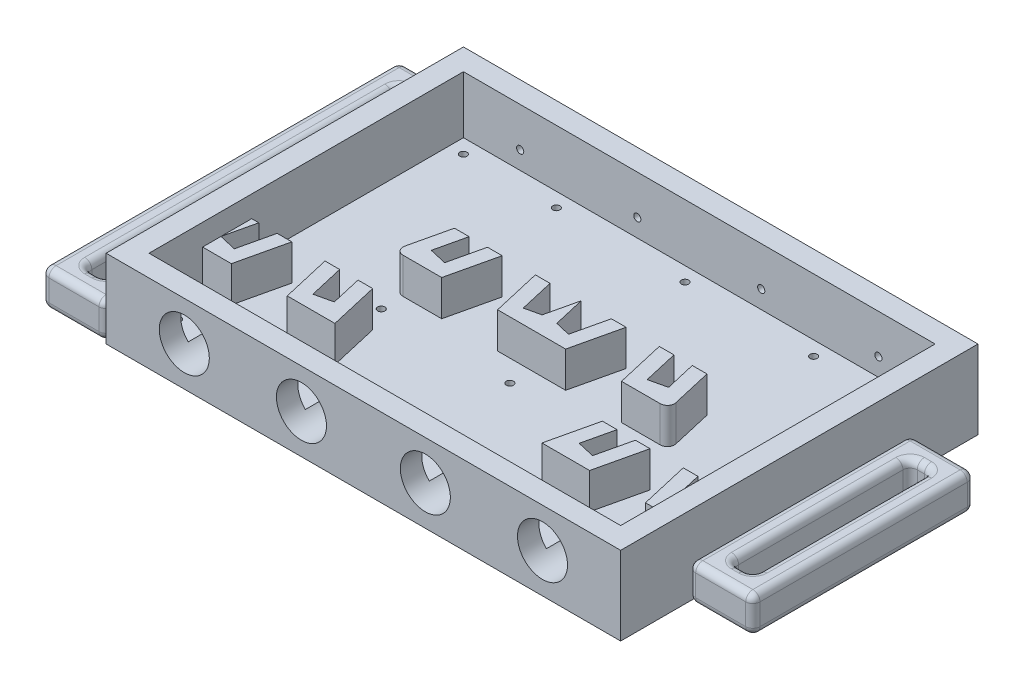
SolidWorks part; units mm, degrees
ref_plane "Front Plane" through (0, 0, 0) normal (0, 0, 1) x (1, 0, 0)
ref_plane "Top Plane" through (0, 0, 0) normal (0, 1, 0) x (1, 0, 0)
ref_plane "Right Plane" through (0, 0, 0) normal (1, 0, 0) x (0, 0, -1)
sketch "Sketch1" plane through (0, 0, 0) normal (0, 1, 0) x (1, 0, 0)
  line L1 (0, 0) -> (72, 0)
  line L2 (0, 0) -> (0, 50)
  line L3 (0, 50) -> (72, 50)
  line L4 (72, 0) -> (72, 50)
extrude "Boss-Extrude2" add sketch "Sketch1" along normal blind 11 contours L3 L4 L1 L2
sketch "Sketch2" plane through (0, 11, 0) normal (0, 1, 0) x (1, 0, 0)
  line L0 (0, 50) -> (72, 50) construction
  line L1 (3, 3) -> (69, 3)
  line L2 (3, 3) -> (3, 47)
  line L3 (3, 47) -> (69, 47)
  line L4 (69, 3) -> (69, 47)
  line L6 (0, 0) -> (72, 0) construction
  line L7 (0, 0) -> (0, 50) construction
  line L8 (72, 0) -> (72, 50) construction
  dimension "D1" = 3
  dimension "D2" = 3
  dimension "D3" = 3
  dimension "D4" = 3
extrude "Cut-Extrude1" cut sketch "Sketch2" against normal blind 8
sketch "Sketch3" plane through (0, 3, 0) normal (0, 1, 0) x (1, 0, 0)
  line L0 (0.3558, 10.5) -> (7.0268, 10.5)
  line L1 (14.8431, 10.5) -> (21.5141, 10.5)
  line L2 (1.9423, 17.3719) -> (8.6133, 17.3719)
  line L3 (13.2566, 17.3719) -> (19.9276, 17.3719)
  line L4 (1.9423, 17.3719) -> (0.3558, 10.5)
  line L5 (8.6133, 17.3719) -> (7.0268, 10.5)
  line L6 (3.9949, 17.3719) -> (3, 13.0624)
  line L7 (3, 13.0624) -> (5.4359, 12.5)
  line L8 (5.4359, 12.5) -> (6.5607, 17.3719)
  line L9 (13.2566, 17.3719) -> (14.8431, 10.5)
  line L10 (19.9276, 17.3719) -> (21.5141, 10.5)
  line L11 (18.8699, 13.0624) -> (14.3709, 32.5498)
  line L12 (17.875, 17.3719) -> (18.8699, 13.0624)
  line L13 (18.8699, 13.0624) -> (16.434, 12.5)
  line L14 (16.434, 12.5) -> (15.3092, 17.3719)
  line L15 (16.7514, 23.5375) -> (23.4224, 23.5375)
  line L16 (31.2406, 23.5375) -> (37.6037, 23.5375)
  line L17 (18.3379, 30.4094) -> (25.0089, 30.4094)
  line L18 (29.6541, 30.4094) -> (36.0172, 30.4094)
  line L19 (18.3379, 30.4094) -> (16.7514, 23.5375)
  line L20 (25.0089, 30.4094) -> (23.4224, 23.5375)
  line L21 (20.3905, 30.4094) -> (19.3956, 26.0999)
  line L22 (19.3956, 26.0999) -> (21.8315, 25.5375)
  line L23 (21.8315, 25.5375) -> (22.9563, 30.4094)
  line L24 (29.6541, 30.4094) -> (31.2406, 23.5375)
  line L25 (36.0172, 30.4094) -> (37.6037, 23.5375)
  line L26 (33.9646, 30.4094) -> (34.9751, 26.0324)
  line L27 (34.9751, 26.0324) -> (32.8315, 25.5375)
  line L28 (32.8315, 25.5375) -> (31.7067, 30.4094)
  line L29 (50.484, 10.5) -> (57.1549, 10.5)
  line L30 (64.9732, 10.5) -> (71.6442, 10.5)
  line L31 (52.0705, 17.3719) -> (58.7414, 17.3719)
  line L32 (63.3867, 17.3719) -> (70.0577, 17.3719)
  line L33 (52.0705, 17.3719) -> (50.484, 10.5)
  line L34 (58.7414, 17.3719) -> (57.1549, 10.5)
  line L35 (54.1231, 17.3719) -> (53.1281, 13.0624)
  line L36 (53.1281, 13.0624) -> (55.5641, 12.5)
  line L37 (55.5641, 12.5) -> (56.6888, 17.3719)
  line L38 (63.3867, 17.3719) -> (64.9732, 10.5)
  line L39 (70.0577, 17.3719) -> (71.6442, 10.5)
  line L40 (68.0051, 17.3719) -> (69, 13.0624)
  line L41 (69, 13.0624) -> (66.5641, 12.5)
  line L42 (66.5641, 12.5) -> (65.4393, 17.3719)
  line L43 (34.3991, 23.5375) -> (40.7622, 23.5375)
  line L44 (48.5805, 23.5375) -> (55.2514, 23.5375)
  line L45 (35.9856, 30.4094) -> (42.3487, 30.4094)
  line L46 (46.994, 30.4094) -> (53.6649, 30.4094)
  line L47 (35.9856, 30.4094) -> (34.3991, 23.5375)
  line L48 (42.3487, 30.4094) -> (40.7622, 23.5375)
  line L49 (38.0382, 30.4094) -> (37.0277, 26.0324)
  line L50 (37.0277, 26.0324) -> (39.1713, 25.5375)
  line L51 (39.1713, 25.5375) -> (40.2961, 30.4094)
  line L52 (46.994, 30.4094) -> (48.5805, 23.5375)
  line L53 (53.6649, 30.4094) -> (55.2514, 23.5375)
  line L54 (51.6123, 30.4094) -> (52.6073, 26.0999)
  line L55 (52.6073, 26.0999) -> (50.1713, 25.5375)
  line L56 (50.1713, 25.5375) -> (49.0466, 30.4094)
  line L57 (3, 47) -> (3, 3) construction
  line L58 (69, 3) -> (69, 47) construction
  line L59 (53.1281, 13.0624) -> (57.6272, 32.5498)
  line L60 (21.8315, 25.5375) -> (26.3305, 45.0249)
  line L61 (50.1713, 25.5375) -> (45.6723, 45.0249)
  line L62 (3, 3) -> (69, 3) construction
  line L64 (5.4359, 12.5) -> (9.9349, 31.9874)
  line L65 (16.434, 12.5) -> (11.9349, 31.9874)
  line L66 (0, 0) -> (0, 50) construction
  line M1 (3, 47) -> (3, 3)
  line M3 (69, 3) -> (69, 47)
  dimension "D2" = 77
  dimension "D3" = 2.5
  dimension "D4" = 2
  dimension "D5" = 2
  dimension "D6" = 2.5
  dimension "D7" = 2
  dimension "D8" = 2
  dimension "D9" = 5
  dimension "D10" = 5
  dimension "D11" = 77
  dimension "D12" = 2
  dimension "D13" = 2
  dimension "D14" = 2.5
  dimension "D15" = 2
  dimension "D16" = 2
  dimension "D17" = 11
  dimension "D18" = 77
  dimension "D19" = 77
  dimension "D20" = 5
  dimension "D21" = 5
  dimension "D22" = 2
  dimension "D23" = 2.2
  dimension "D24" = 2
  dimension "D25" = 11
  dimension "D26" = 2
  dimension "D27" = 2
  dimension "D28" = 2.2
  dimension "D29" = 77
  dimension "D30" = 5
  dimension "D31" = 5
  dimension "D32" = 77
  dimension "D33" = 2
  dimension "D34" = 2
  dimension "D35" = 2.5
  dimension "D36" = 77
  dimension "D37" = 2
  dimension "D38" = 2
  dimension "D39" = 2.5
  dimension "D40" = 2.5
  dimension "D41" = 2
  dimension "D42" = 2
  dimension "D43" = 11
  dimension "D44" = 77
  dimension "D45" = 5
  dimension "D46" = 5
  dimension "D47" = 2
  dimension "D48" = 2
  dimension "D49" = 7.5
  dimension "D50" = 7.5
  dimension "D51" = 3.49
  dimension "D52" = 3.4948
  dimension "D53" = 5.4359
  dimension "D54" = 21.8315
  dimension "D55" = 2
  dimension "D56" = 20
  dimension "D57" = 20
  dimension "D58" = 20
  dimension "D59" = 20
  dimension "D60" = 20
  dimension "D61" = 20
  dimension "D62" = 10.998
extrude "Boss-Extrude3" add sketch "Sketch3" along normal blind 5 contours L8 L7 L0 L5 L2 M1 | L13 L14 L3 L9 L1 L10 L11 | L23 L22 L21 L17 L19 L15 L20 | L51 L50 L25 L43 L48 L45 | L55 L56 L46 L52 L44 L53 L54 | L37 L36 L35 L31 L33 L29 L34 | L41 L42 L32 L38 L30 M3 | L47 L27 L28 L18 L24 L16 | L18 L47 L16 L25 | L6 L2 M1 | L32 L40 M3
sketch "Sketch4" plane through (0, 0, 0) normal (0, 0, 1) x (1, 0, 0)
  line L0 (3, 3) -> (69, 3) construction
  line L2 (0, 11) -> (72, 11) construction
  line L3 (0, 11) -> (0, 0) construction
  line L4 (72, 11) -> (72, 0) construction
  circle A0 centre (10.94, 5.5) radius 3.5
  circle A1 centre (27.33, 5.5) radius 3.5
  circle A2 centre (44.67, 5.5) radius 3.5
  circle A3 centre (61.06, 5.5) radius 3.5
  dimension "D1" = 2.5
  dimension "D2" = 5.5
  dimension "D3" = 5.5
  dimension "D4" = 5.5
  dimension "D5" = 10.94
  dimension "D6" = 10.94
  dimension "D8" = 27.33
  dimension "D7" = 27.33
extrude "Cut-Extrude3" cut sketch "Sketch4" against normal blind 10
sketch "Sketch10" plane through (0, 0, -50) normal (0, 0, 1) x (1, 0, 0)
  circle A0 centre (10.94, 5.5) radius 3.5
  circle A1 centre (27.33, 5.5) radius 3.5
  circle A2 centre (44.67, 5.5) radius 3.5
  circle A3 centre (61.06, 5.5) radius 3.5
extrude "Cut-Extrude9" cut sketch "Sketch10" along normal blind 1.5
sketch "Sketch6" plane through (0, 0, -48.5) normal (0, 0, 1) x (1, 0, 0)
  circle A0 centre (10.94, 5.5) radius 0.5
  circle A1 centre (27.33, 5.5) radius 0.5
  circle A2 centre (44.67, 5.5) radius 0.5
  circle A3 centre (61.06, 5.5) radius 0.5
extrude "Cut-Extrude5" cut sketch "Sketch6" along normal blind 1.5
sketch "Sketch8" plane through (0, 0, 0) normal (0, -1, 0) x (-1, 0, 0)
  line L0 (-72, 0) -> (-72, 50) construction
  line L1 (0, 0) -> (9, 0)
  line L2 (0, 0) -> (0, 50)
  line L3 (0, 50) -> (9, 50)
  line L4 (9, 0) -> (9, 50)
  line L5 (3, 47) -> (6, 47)
  line L6 (3, 47) -> (3, 3)
  line L7 (3, 3) -> (6, 3)
  line L8 (6, 47) -> (6, 3)
  line L17 (-72, 40.5) -> (-81, 40.5)
  line L18 (-72, 40.5) -> (-72, 9.5)
  line L19 (-72, 9.5) -> (-81, 9.5)
  line L20 (-81, 40.5) -> (-81, 9.5)
  line L21 (-78, 12.5) -> (-75, 12.5)
  line L22 (-78, 12.5) -> (-78, 37.5)
  line L23 (-78, 37.5) -> (-75, 37.5)
  line L24 (-75, 12.5) -> (-75, 37.5)
  dimension "D1" = 3
  dimension "D2" = 3
  dimension "D3" = 3
  dimension "D4" = 3
  dimension "D5" = 25
  dimension "D6" = 3
  dimension "D7" = 3
  dimension "D8" = 3
  dimension "D9" = 3
  dimension "D10" = 3
  dimension "D11" = 9.5
  dimension "D12" = 9.5
  dimension "D13" = 3
extrude "Boss-Extrude4" add sketch "Sketch8" against normal blind 5 separate body
fillet "Fillet1" radius 1 24 edges at (72, 2.5, -9.5) (78, 2.5, -37.5) (78, 2.5, -12.5) (75, 2.5, -12.5) (75, 2.5, -37.5) (76.5, 0, -9.5) (72, 0, -25) (75, 0, -25) (76.5, 0, -37.5) (78, 0, -25) (76.5, 0, -12.5) (72, 2.5, -40.5) (76.5, 0, -40.5) (81, 2.5, -9.5) (81, 2.5, -40.5) (81, 0, -25) (76.5, 5, -40.5) (81, 5, -25) (76.5, 5, -9.5) (72, 5, -25) (76.5, 5, -37.5) (75, 5, -25) (76.5, 5, -12.5) (78, 5, -25)
fillet "Fillet2" radius 1 24 edges at (-3, 2.5, -47) (-4.5, 0, -47) (-3, 0, -25) (-4.5, 5, -47) (-3, 5, -25) (-3, 2.5, -3) (-4.5, 5, -3) (-4.5, 0, -3) (-6, 2.5, -3) (-6, 5, -25) (-6, 2.5, -47) (-6, 0, -25) (-4.5, 5, 0) (0, 2.5, 0) (-4.5, 0, 0) (-9, 2.5, -50) (-9, 5, -25) (-9, 2.5, 0) (-9, 0, -25) (0, 2.5, -50) (-4.5, 5, -50) (0, 5, -25) (-4.5, 0, -50) (0, 0, -25)
fillet "Fillet3" radius 1 2 edges at (16.7514, 5.5, -23.5375) (55.2514, 5.5, -23.5375)
sketch "Sketch11" plane through (0, 3, 0) normal (0, 1, 0) x (1, 0, 0)
  line L0 (69, 47) -> (3, 47) construction
  line L1 (3, 47) -> (3, 3) construction
  line L2 (69, 17.3719) -> (69, 47) construction
  line L3 (69, 47) -> (3, 47) construction
  line L4 (69, 3) -> (69, 10.5) construction
  line L5 (3, 3) -> (69, 3) construction
  line L6 (29.7795, 3) -> (42.2205, 3) construction
  line L7 (13.3895, 3) -> (24.8805, 3) construction
  line L8 (3, 3) -> (8.4905, 3) construction
  line L9 (3, 47) -> (3, 17.3719) construction
  line L10 (69, 3) -> (69, 47) construction
  line L11 (47.1195, 3) -> (58.6105, 3) construction
  circle A0 centre (5, 45) radius 0.5
  circle A1 centre (18, 45) radius 0.5
  circle A2 centre (36, 45) radius 0.5
  circle A3 centre (54, 45) radius 0.5
  circle A4 centre (67, 45) radius 0.5
  circle A5 centre (5, 5) radius 0.5
  circle A6 centre (18, 5) radius 0.5
  circle A7 centre (36, 5) radius 0.5
  circle A8 centre (54, 5) radius 0.5
  circle A9 centre (67, 5) radius 0.5
  circle A10 centre (18, 20.5) radius 0.5
  circle A11 centre (36, 20.5) radius 0.5
  circle A12 centre (54, 20.5) radius 0.5
  dimension "D1" = 2
  dimension "D3" = 2
  dimension "D4" = 15
  dimension "D5" = 33
  dimension "D6" = 33
  dimension "D8" = 2
  dimension "D9" = 2
  dimension "D10" = 2
  dimension "D15" = 2
  dimension "D16" = 2
  dimension "D17" = 2
  dimension "D19" = 15
  dimension "D21" = 2
  dimension "D22" = 15
  dimension "D25" = 17.5
  dimension "D26" = 17.5
  dimension "D27" = 17.5
  dimension "D2" = 2
  dimension "D7" = 15
  dimension "D11" = 2
  dimension "D12" = 15
  dimension "D13" = 33
  dimension "D14" = 2
  dimension "D18" = 2
  dimension "D20" = 2
  dimension "D23" = 15
  dimension "D24" = 33
extrude "Cut-Extrude10" cut sketch "Sketch11" against normal blind 3
